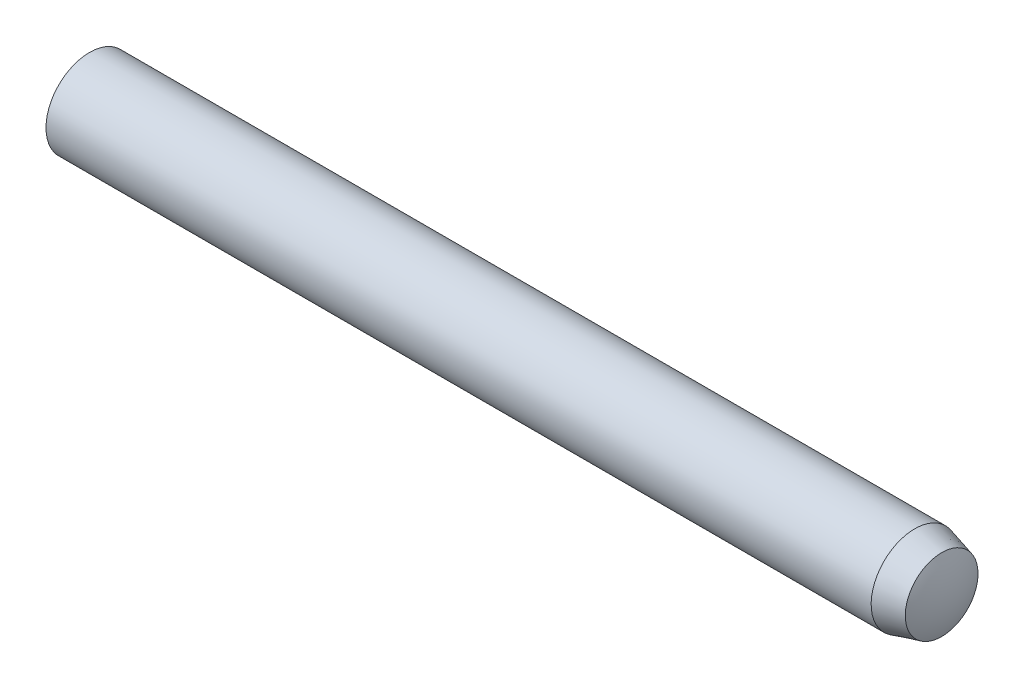
SolidWorks part; units mm, degrees
ref_plane "Plane1" through (0, 0, 0) normal (0, 0, 1) x (1, 0, 0)
ref_plane "Plane2" through (0, 0, 0) normal (0, 1, 0) x (1, 0, 0)
ref_plane "Plane3" through (0, 0, 0) normal (1, 0, 0) x (0, 0, -1)
sketch "BodySke" plane through (0, 0, 0) normal (0, 0, 1) x (1, 0, 0)
  line L0 (0, 0) -> (40.9091, 0) construction
  line L1 (28.8, 1.5) -> (29.7264, 1.2518)
  line L2 (0.4, 1.5) -> (28.8, 1.5)
  line L4 (0, 0) -> (30, 0)
  arc A0 (0.4, 1.5) -> (0, 0) centre (3.0125, 0) ccw
  arc A1 (30, 0) -> (29.7264, 1.2518) centre (27, 0) ccw
  dimension "TipRad" = 3
  dimension "D1" = 15
  dimension "Diameter" = 3
  dimension "Crown_ht" = 0.4
  dimension "Length" = 30
  dimension "Chamfer_len" = 1.2
revolve "Body" add sketch "BodySke" angle 360 about L0
equation "\"TipRad@BodySke\" = \"Diameter@BodySke\""
